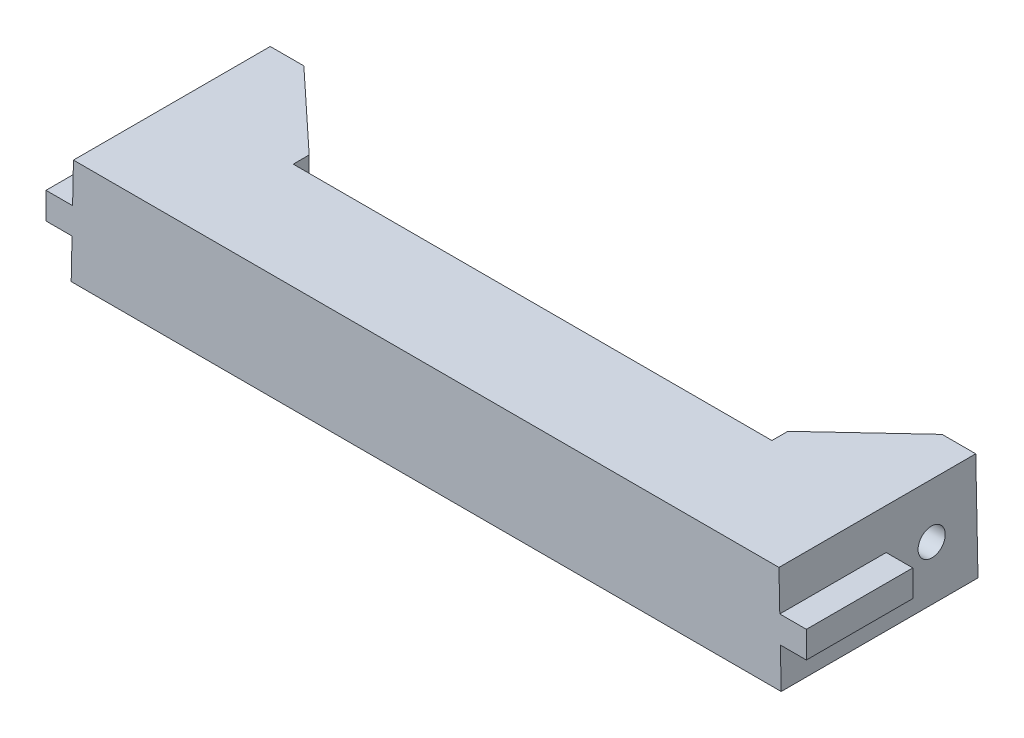
SolidWorks part; units mm, degrees
ref_plane "Front Plane" through (0, 0, 0) normal (0, 0, 1) x (1, 0, 0)
ref_plane "Top Plane" through (0, 0, 0) normal (0, 1, 0) x (1, 0, 0)
ref_plane "Right Plane" through (0, 0, 0) normal (1, 0, 0) x (0, 0, -1)
sketch "Sketch1" plane through (0, 0, 0) normal (0, 0, 1) x (1, 0, 0)
  line L0 (-66.745, 0) -> (66.745, 0)
  line L1 (-66.745, 0) -> (-66.3208, 20)
  line L2 (-66.3208, 20) -> (66.3208, 20)
  line L3 (66.3208, 20) -> (66.745, 0)
  point P4 (0, 0)
  point P8 (0, 20)
  dimension "D1" = 20
  dimension "D2" = 2.43
  dimension "D3" = 133.49
extrude "Boss-Extrude1" add sketch "Sketch1" along normal blind 20
sketch "Sketch2" plane through (66.715, 1.415, 0) normal (0.9998, 0.0212, 0) x (0, 0, -1)
  line L0 (-20, -1.4153) -> (0, -1.4153) construction
  line L5 (0, 18.5892) -> (17, 18.5892)
  line L6 (0, 18.5892) -> (0, -1.4153)
  line L7 (0, -1.4153) -> (17, -1.4153)
  line L8 (17, 18.5892) -> (17, -1.4153)
  line L9 (0, 8.587) -> (17, 8.587) construction
  circle A0 centre (8.5, 8.587) radius 2.55
  dimension "D2" = 5.1
  dimension "D1" = 17
ref_plane "Plane1" through (60, 0, 0) normal (1, 0, 0) x (0, 0, -1)
sketch "Sketch3" plane through (60, 0, 0) normal (1, 0, 0) x (0, 0, -1)
  line L1 (0, 20) -> (17, 20)
  line L2 (0, 20) -> (0, 0)
  line L3 (0, 0) -> (17, 0)
  line L4 (17, 20) -> (17, 0)
  line L8 (17, 20) -> (17, 0) construction
loft "Loft1" add profiles "Sketch3" section "Sketch3" section "Sketch2"
sketch "Sketch5" plane through (0, 0, 20) normal (0, 0, 1) x (1, 0, 0)
  line L0 (66.745, 0) -> (66.3208, 20) construction
  line L1 (66.4799, 12.5) -> (71.4799, 12.5)
  line L2 (66.4799, 12.5) -> (66.4799, 7.5)
  line L3 (66.4799, 7.5) -> (71.4799, 7.5)
  line L4 (71.4799, 12.5) -> (71.4799, 7.5)
  line L5 (0, 0) -> (0, 20) construction
  line L6 (66.3208, 20) -> (-66.3208, 20) construction
  line L7 (0, 10) -> (66.4799, 10) construction
  dimension "D1" = 5
  dimension "D2" = 5
extrude "Boss-Extrude2" add sketch "Sketch5" against normal up to surface (20 mm away) up to face at (-3.3195, 12.5, 0)
mirror "Mirror2" about plane through (0, 0, 0) normal (1, 0, 0) of "Boss-Extrude2"
ref_plane "Plane2" through (45, 0, 0) normal (1, 0, 0) x (0, 0, -1)
sketch "Sketch6" plane through (60, 0, 0) normal (-1, 0, 0) x (0, 0, 1)
  line L0 (0, 20) -> (0, 0)
  line L1 (0, 12.5) -> (0, 7.5) construction
  line L2 (0, 10) -> (-8.5, 10) construction
  line L3 (-8.5, 20) -> (-8.5, 10) construction
  line L4 (-17, 20) -> (0, 20) construction
  circle A0 centre (-8.5, 10) radius 2.55
  point P15 (0, 10)
  dimension "D1" = 5.1
extrude "Cut-Extrude1" cut sketch "Sketch6" against normal through all contours A0
sketch "Sketch7" plane through (45, 0, 0) normal (1, 0, 0) x (0, 0, -1)
  line L0 (0, 20) -> (0, 0)
  line L1 (0, 0) -> (3, 0)
  line L2 (0, 0) -> (17, 0) construction
  line L3 (3, 0) -> (3, 20)
  line L4 (17, 20) -> (0, 20) construction
  line L5 (3, 20) -> (0, 20)
  dimension "D1" = 3
sketch "Sketch8" plane through (60, 0, 0) normal (-1, 0, 0) x (0, 0, 1)
  line L4 (0, 0) -> (0, 20)
  line L5 (0, 20) -> (-17, 20)
  line L6 (-17, 20) -> (-17, 0)
  line L7 (-17, 0) -> (0, 0)
  line L8 (0, 0) -> (0, 20)
  line L9 (0, 20) -> (-17, 20)
  line L10 (-17, 20) -> (-17, 0)
  line L11 (-17, 0) -> (0, 0)
  dimension "D1" = 0
loft "Loft2" add profiles "Sketch8", "Sketch7"
sketch "Sketch9" plane through (60, 0, 0) normal (1, 0, 0) x (0, 0, -1)
  circle A0 centre (8.5, 10) radius 6.5
  dimension "D1" = 13
extrude "Cut-Extrude2" cut sketch "Sketch9" against normal blind 30
mirror "Mirror3" about plane through (0, 0, 0) normal (1, 0, 0) of "Cut-Extrude2", "Loft2", "Cut-Extrude1", "Loft1"
